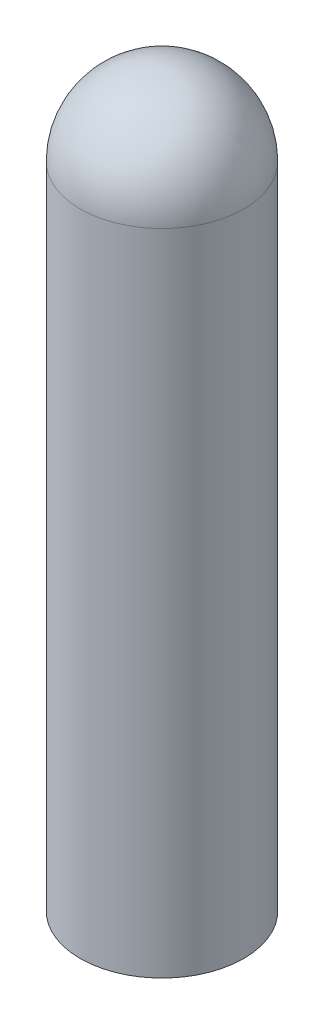
SolidWorks part; units mm, degrees
material "Rubber"
ref_plane "Front Plane" through (0, 0, 0) normal (0, 0, 1) x (1, 0, 0)
ref_plane "Top Plane" through (0, 0, 0) normal (0, 1, 0) x (1, 0, 0)
ref_plane "Right Plane" through (0, 0, 0) normal (1, 0, 0) x (0, 0, -1)
sketch "Sketch1" plane through (0, 0, 0) normal (0, 0, 1) x (1, 0, 0)
  line L0 (-3.556, 0) -> (-3.556, 28.194)
  line L1 (0, 0) -> (0, -6.35) construction
  line L2 (0, -55) -> (0, 55) construction
  line L3 (-3.556, 0) -> (0, 0)
  line L4 (0, 0) -> (0, 31.75)
  arc A0 (-3.556, 28.194) -> (0, 31.75) centre (0, 28.194) cw
  dimension "D1" = 31.75
  dimension "D2" = 7.112
  dimension "D3" = 6.35
  dimension "D4" = 28.194
revolve "Revolve1" add sketch "Sketch1" angle 360 about L1
sketch "Sketch2" plane through (0, 0, 0) normal (0, -1, 0) x (1, 0, 0)
  circle A0 centre (0, 0) radius 3.175
  dimension "D1" = 6.35
extrude "Cut-Extrude1" cut sketch "Sketch2" against normal blind 28.575
